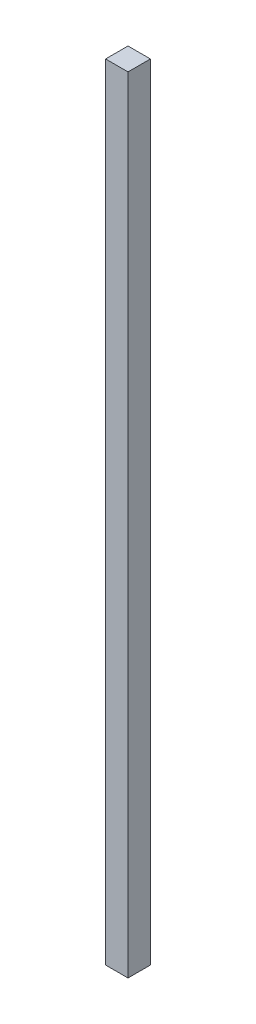
SolidWorks part; units mm, degrees
material "Balsa"
ref_plane "Front Plane" through (0, 0, 0) normal (0, 0, 1) x (1, 0, 0)
ref_plane "Top Plane" through (0, 0, 0) normal (0, 1, 0) x (1, 0, 0)
ref_plane "Right Plane" through (0, 0, 0) normal (1, 0, 0) x (0, 0, -1)
sketch "Sketch1" plane through (0, 0, 0) normal (0, 1, 0) x (1, 0, 0)
  line L1 (-5, 5) -> (5, 5)
  line L2 (-5, 5) -> (-5, -5)
  line L3 (-5, -5) -> (5, -5)
  line L4 (5, 5) -> (5, -5)
  line L5 (-5, 5) -> (5, -5) construction
  line L6 (-5, -5) -> (5, 5) construction
  point P0 (0, 0)
  dimension "D1" = 10
  dimension "D2" = 10
extrude "Boss-Extrude1" add sketch "Sketch1" along normal blind 350
